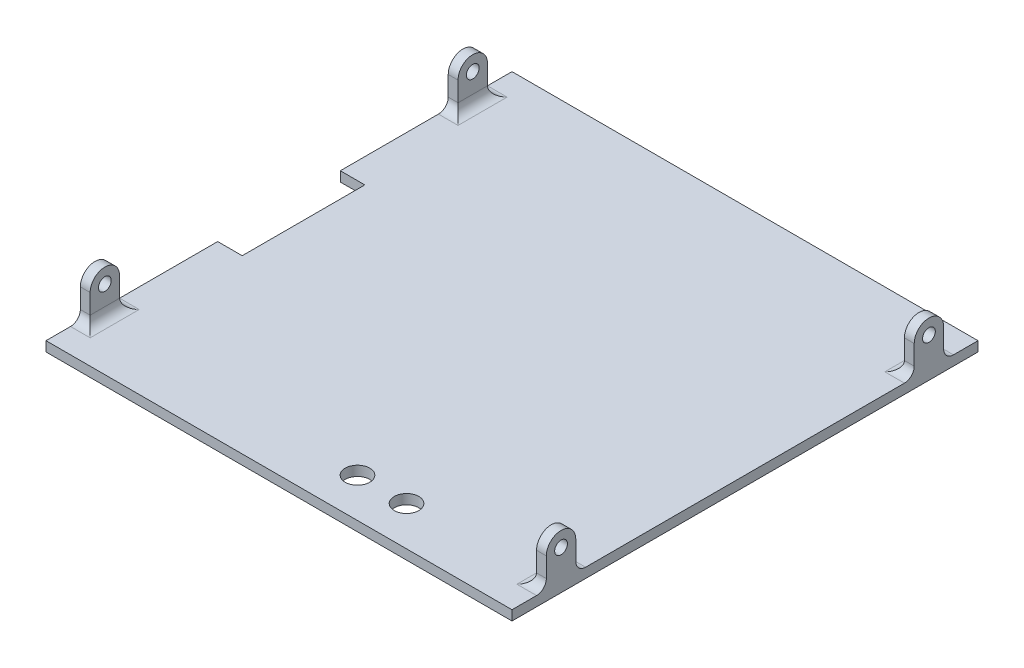
SolidWorks part; units mm, degrees
ref_plane "Front Plane" through (0, 0, 0) normal (0, 0, 1) x (1, 0, 0)
ref_plane "Top Plane" through (0, 0, 0) normal (0, 1, 0) x (1, 0, 0)
ref_plane "Right Plane" through (0, 0, 0) normal (1, 0, 0) x (0, 0, -1)
sketch "Sketch1" plane through (0, 0, 0) normal (0, 1, 0) x (1, 0, 0)
  line L1 (-47.5, 47.5) -> (47.5, 47.5)
  line L2 (-47.5, 47.5) -> (-47.5, -47.5)
  line L3 (-47.5, -47.5) -> (47.5, -47.5)
  line L4 (47.5, 47.5) -> (47.5, -47.5)
  line L5 (-47.5, 47.5) -> (47.5, -47.5) construction
  line L6 (-47.5, -47.5) -> (47.5, 47.5) construction
  point P0 (0, 0)
  dimension "D1" = 95
  dimension "D2" = 95
extrude "Boss-Extrude1" add sketch "Sketch1" along normal blind 2
sketch "Sketch2" plane through (0, 2, 0) normal (0, 1, 0) x (1, 0, 0)
  line L0 (-47.5, 47.5) -> (-47.5, -47.5) construction
  line L1 (-47.5, -40.5) -> (-45.5, -40.5)
  line L2 (-47.5, -40.5) -> (-47.5, -34.5)
  line L3 (-47.5, -34.5) -> (-45.5, -34.5)
  line L4 (-45.5, -40.5) -> (-45.5, -34.5)
  line L5 (-47.5, -47.5) -> (47.5, -47.5) construction
  line L6 (47.5, 47.5) -> (-47.5, 47.5) construction
  line L7 (-47.5, 40.5) -> (-45.5, 40.5)
  line L8 (-47.5, 40.5) -> (-47.5, 34.5)
  line L9 (-47.5, 34.5) -> (-45.5, 34.5)
  line L10 (-45.5, 40.5) -> (-45.5, 34.5)
  line L11 (0, 0) -> (0, 23.6676) construction
  line L12 (47.5, -34.5) -> (45.5, -34.5)
  line L13 (45.5, -40.5) -> (45.5, -34.5)
  line L14 (47.5, -40.5) -> (45.5, -40.5)
  line L15 (47.5, -40.5) -> (47.5, -34.5)
  line L16 (47.5, 34.5) -> (45.5, 34.5)
  line L17 (45.5, 40.5) -> (45.5, 34.5)
  line L18 (47.5, 40.5) -> (45.5, 40.5)
  line L19 (47.5, 40.5) -> (47.5, 34.5)
  dimension "D1" = 6
  dimension "D2" = 2
  dimension "D3" = 7
  dimension "D4" = 2
  dimension "D5" = 7
  dimension "D6" = 6
extrude "Boss-Extrude2" add sketch "Sketch2" along normal blind 6
sketch "Sketch3" plane through (-45.5, 0, 0) normal (1, 0, 0) x (0, 0, -1)
  line L0 (-40.5, 8) -> (-34.5, 8) construction
  line L1 (0, 0) -> (0, 11.2321) construction
  circle A0 centre (-37.5, 8) radius 3
  circle A1 centre (37.5, 8) radius 3
extrude "Boss-Extrude3" add sketch "Sketch3" against normal blind 2
sketch "Sketch6" plane through (45.5, 0, 0) normal (-1, 0, 0) x (0, 0, 1)
  line L0 (-40.5, 8) -> (-34.5, 8) construction
  line L1 (34.5, 8) -> (40.5, 8) construction
  circle A0 centre (-37.5, 8) radius 3
  circle A1 centre (37.5, 8) radius 3
extrude "Boss-Extrude5" add sketch "Sketch6" against normal blind 2
sketch "Sketch8" plane through (-47.5, 0, 0) normal (-1, 0, 0) x (0, 0, 1)
  circle A0 centre (-37.5, 8) radius 1.3
  circle A1 centre (37.5, 8) radius 1.3
  dimension "D1" = 2.6
  dimension "D2" = 2.6
extrude "Cut-Extrude2" cut sketch "Sketch8" against normal through all
fillet "Fillet1" radius 2 12 edges at (46.5, 2, 40.5) (46.5, 2, -34.5) (45.5, 2, 37.5) (46.5, 2, 34.5) (45.5, 2, -37.5) (46.5, 2, -40.5) (-46.5, 2, 34.5) (-45.5, 2, 37.5) (-46.5, 2, 40.5) (-46.5, 2, -40.5) (-45.5, 2, -37.5) (-46.5, 2, -34.5)
sketch "Sketch10" plane through (-47.5, 0, 0) normal (-1, 0, 0) x (0, 0, 1)
  line L0 (-32.5, 2) -> (32.5, 2) construction
  line L1 (-12.5, -2) -> (12.5, -2)
  line L2 (-12.5, -2) -> (-12.5, 2)
  line L3 (-12.5, 2) -> (12.5, 2)
  line L4 (12.5, -2) -> (12.5, 2)
  line L5 (-12.5, -2) -> (12.5, 2) construction
  line L6 (-12.5, 2) -> (12.5, -2) construction
  point P0 (0, 0)
  dimension "D1" = 25
extrude "Cut-Extrude3" cut sketch "Sketch10" against normal blind 5
sketch "Sketch11" plane through (0, 2, 0) normal (0, 1, 0) x (1, 0, 0)
  line L0 (0, -13.4005) -> (0, -42.9312) construction
  line L1 (-47.5, -47.5) -> (47.5, -47.5) construction
  circle A0 centre (18, -39.5) radius 2.5
  circle A1 centre (8, -39.5) radius 2.5
  dimension "D1" = 5
  dimension "D2" = 5
  dimension "D3" = 8
  dimension "D5" = 8
  dimension "D6" = 8
  dimension "D4" = 18
extrude "Cut-Extrude4" cut sketch "Sketch11" against normal blind 2
